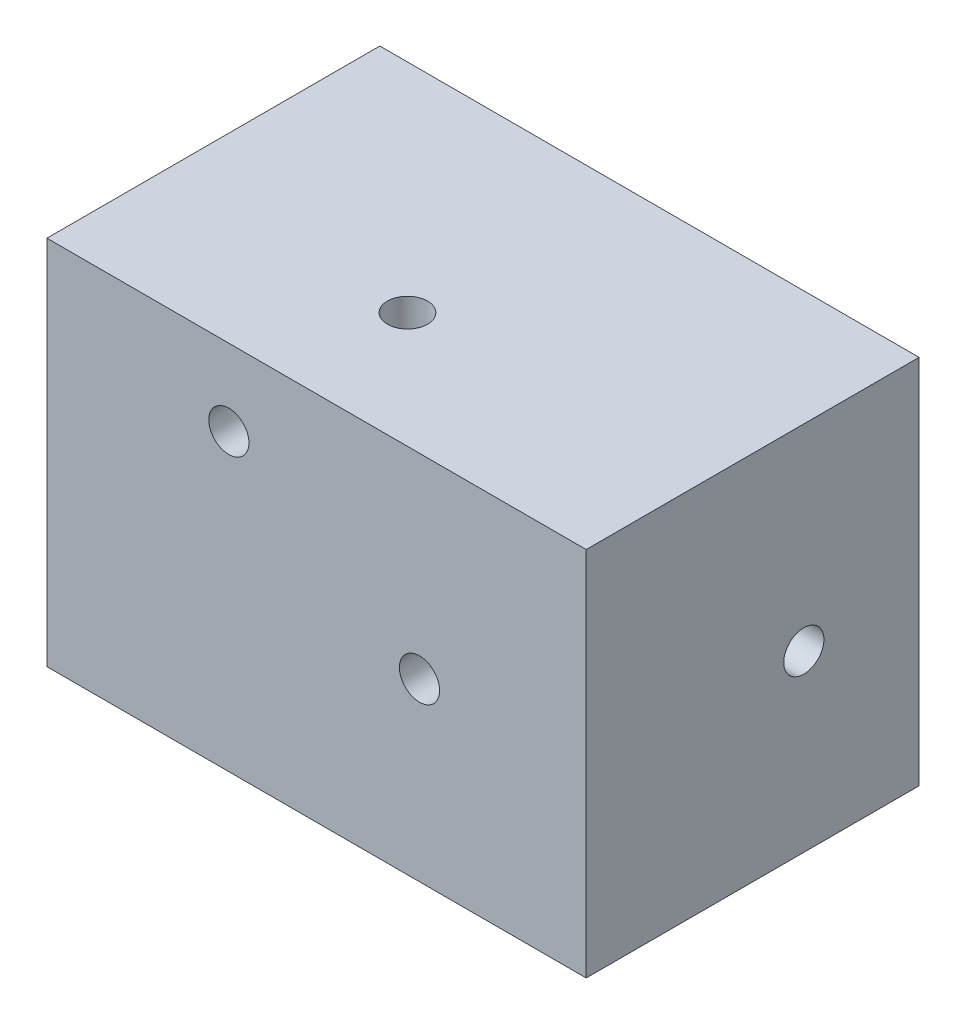
SolidWorks part; units mm, degrees
ref_plane "Front Plane XY" through (0, 0, 0) normal (0, 0, 1) x (1, 0, 0)
ref_plane "Top Plane XZ" through (0, 0, 0) normal (0, 1, 0) x (1, 0, 0)
ref_plane "Right Plane YZ" through (0, 0, 0) normal (1, 0, 0) x (0, 0, -1)
sketch "Sketch1" plane through (0, 0, 0) normal (0, 0, 1) x (1, 0, 0)
  line L1 (-66.5133, 43.5261) -> (70.3877, 43.5261)
  line L2 (-66.5133, 43.5261) -> (-66.5133, -50.6735)
  line L3 (-66.5133, -50.6735) -> (70.3877, -50.6735)
  line L4 (70.3877, 43.5261) -> (70.3877, -50.6735)
extrude "Extrude1" add sketch "Sketch1" along normal blind 84.5
hole_wizard "M12 Tapped Hole1" positions "3DSketch1" profile "Sketch2" tap size "M12" standard "ISO"
sketch3d "3DSketch1"
  point P0 (-4.3812, 43.5261, 55.1138)
  point P2 (-20.3301, 24.1488, 84.5)
  point P4 (28.0635, -6.1018, 84.5)
  point P6 (70.3877, -6.3904, 29.2573)
  point P8 (37.2931, -19.3921, 0)
sketch "Sketch2" plane through (-4.3812, 43.5261, 55.1138) normal (1, 0, 0) x (0, 0, 1)
  line L0 (0, 0) -> (0, 35.8144)
  line L1 (3.3834, 33.7814) -> (5.1, 32.75)
  line L2 (5.1, 32.75) -> (5.1, 0)
  line L3 (3.3834, 33.7814) -> (3.3834, 43.5261)
  line L4 (3.3834, 43.5261) -> (0, 46.4494)
  line L5 (5.1, 0) -> (0, 0)
  line L6 (0, 46.4494) -> (0, 35.8144)
  line L10 (0, 35.8144) -> (-5.1, 32.75) construction
  line L11 (0, -6.35) -> (0, 107.95) construction
  dimension "Průměr závitníku" = 10.2
  dimension "Hloubka závitníku" = 32.75
  dimension "Úhel vrtání" = 118
cosmetic thread "Cosmetic Thread1"
cosmetic thread "Cosmetic Thread2"
cosmetic thread "Cosmetic Thread3"
cosmetic thread "Cosmetic Thread4"
cosmetic thread "Cosmetic Thread5"
